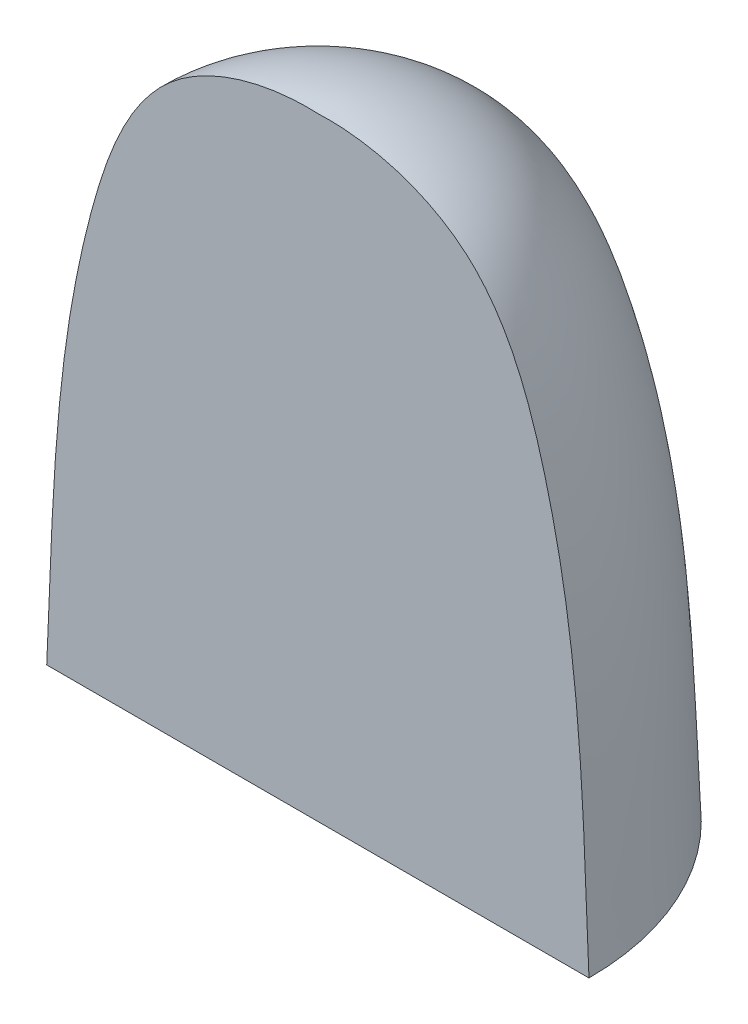
SolidWorks part; units mm, degrees
ref_plane "Plan de face" through (0, 0, 0) normal (0, 0, 1) x (1, 0, 0)
ref_plane "Plan de dessus" through (0, 0, 0) normal (0, 1, 0) x (1, 0, 0)
ref_plane "Plan de droite" through (0, 0, 0) normal (1, 0, 0) x (0, 0, -1)
sketch "Sketch1" plane through (0, 0, 0) normal (0, 0, 1) x (1, 0, 0)
  line L0 (0, 24.0802) -> (0, -22.399) construction
  line L1 (-32.5945, 0) -> (42.86, 0) construction
  line L2 (6.5, 0) -> (9, 0)
  line L3 (0, 20.35) -> (0, 17.85)
  spline S0 degree 3 poles (0, 20.35) (1.676, 20.4282) (5.6604, 19.3725) (8.7405, 10.942) (8.7941, 4.7856) (9, 0) knots 0 0 0 0 0.209087 0.440429 1 1 1 1
  spline S1 degree 3 poles (0, 17.85) (1.2485, 18.0031) (3.4343, 16.8333) (6.6173, 10.5141) (6.2204, 4.5323) (6.5, 0) knots 0 0 0 0 0.174731 0.328982 1 1 1 1
  dimension "D1" = 17.85
  dimension "D2" = 2.5
  dimension "D3" = 2.5
  dimension "D4" = 9
revolve "Revolve1" add sketch "Sketch1" angle 360 about L0
ref_plane "Plane1" through (0, 0, 9) normal (0, 0, 1) x (1, 0, 0)
sketch "Sketch2" plane through (0, 0, 9) normal (0, 0, 1) x (1, 0, 0)
  line L1 (11.948, 23.5635) -> (-10.2198, 23.5635)
  line L2 (11.948, 23.5635) -> (11.948, -1.5483)
  line L3 (11.948, -1.5483) -> (-10.2198, -1.5483)
  line L4 (-10.2198, 23.5635) -> (-10.2198, -1.5483)
extrude "Cut-Extrude1" cut sketch "Sketch2" against normal blind 9
sketch "Sketch3" plane through (0, 0, 0) normal (0, 0, 1) x (1, 0, 0)
  line L0 (-6.5, 0) -> (-9, 0) construction
  line L1 (9, 0) -> (6.5, 0) construction
  line L2 (-7.75, 0) -> (7.75, 0)
  spline S0 degree 3 poles (-7.75, 0) (-8.0037, 4.4913) (-7.6617, 10.4833) (-4.6624, 18.2746) (0.1487, 19.6172) (4.6774, 17.8832) (7.7739, 10.3963) (7.4113, 4.3412) (7.75, 0) knots 0 0 0 0 0.289464 0.419224 0.50187 0.592484 0.714941 1 1 1 1
  point P2 (0, 0)
extrude "Boss-Extrude1" add sketch "Sketch3" against normal blind 1
